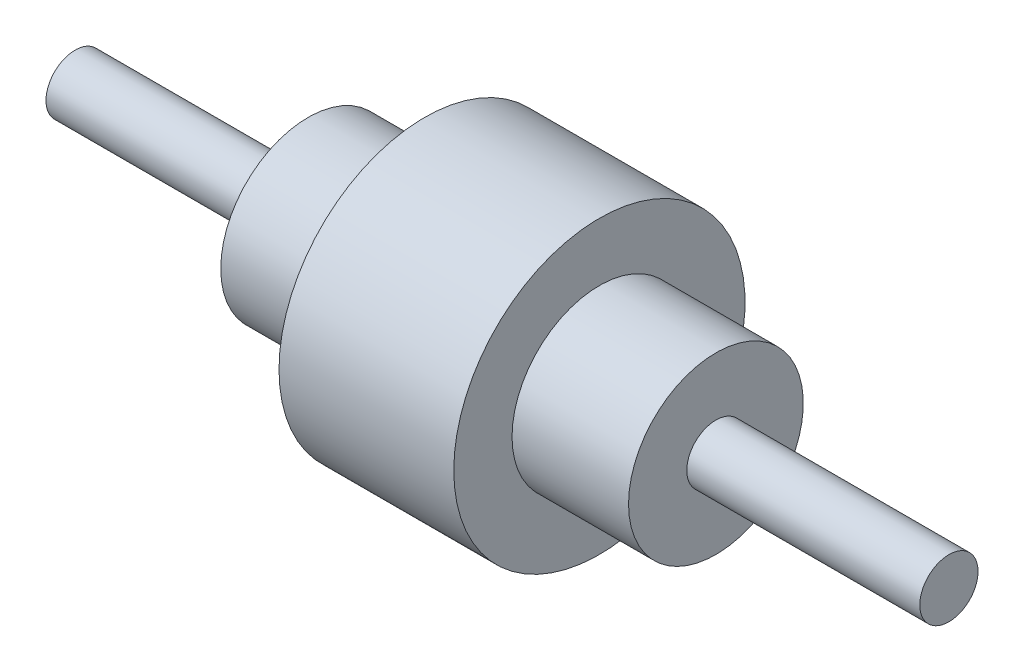
SolidWorks part; units mm, degrees
ref_plane "Front Plane" through (0, 0, 0) normal (0, 0, 1) x (1, 0, 0)
ref_plane "Top Plane" through (0, 0, 0) normal (0, 1, 0) x (1, 0, 0)
ref_plane "Right Plane" through (0, 0, 0) normal (1, 0, 0) x (0, 0, -1)
sketch "Sketch2" plane through (0, 0, 0) normal (0, 1, 0) x (1, 0, 0)
  line L0 (-169.6386, 0) -> (274.2169, 0) construction
  line L2 (30, 50) -> (-30, 50)
  line L3 (-30, 50) -> (-30, 30)
  line L4 (-30, 30) -> (-70, 30)
  line L5 (-70, 30) -> (-70, 10)
  line L6 (-70, 10) -> (-150, 10)
  line L7 (-150, 10) -> (-150, 0)
  line L8 (-150, 0) -> (150, 0)
  line L9 (150, 10) -> (150, 0)
  line L10 (70, 10) -> (150, 10)
  line L11 (70, 30) -> (70, 10)
  line L12 (30, 30) -> (70, 30)
  line L13 (30, 50) -> (30, 30)
  dimension "D1" = 80
  dimension "D2" = 40
  dimension "D3" = 300
  dimension "D4" = 10
  dimension "D5" = 30
  dimension "D6" = 50
revolve "Revolve1" add sketch "Sketch2" angle 360 about L0
